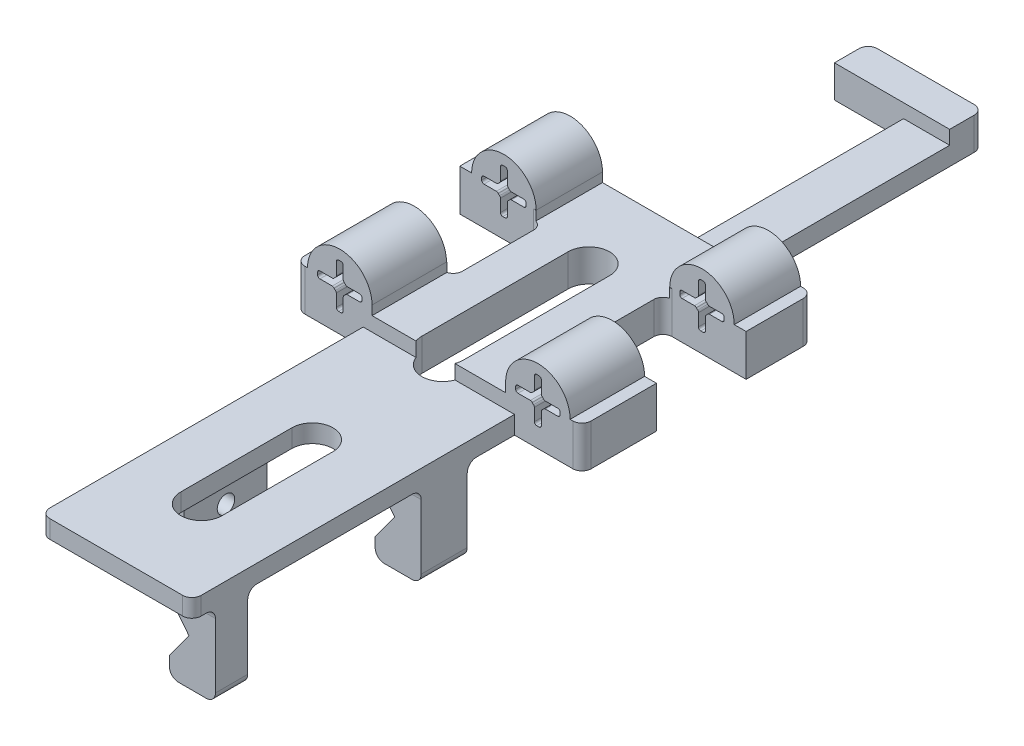
SolidWorks part; units mm, degrees
ref_plane "Спереди" through (0, 0, 0) normal (0, 0, 1) x (1, 0, 0)
ref_plane "Сверху" through (0, 0, 0) normal (0, 1, 0) x (1, 0, 0)
ref_plane "Справа" through (0, 0, 0) normal (1, 0, 0) x (0, 0, -1)
sketch "Эскиз1" plane through (0, 0, 0) normal (0, 0, 1) x (1, 0, 0)
  line L1 (23.3172, -4.25) -> (20.6248, -4.25)
  line L2 (23.8172, -5) -> (23.8172, -4.75)
  line L3 (23.8172, -4.75) -> (23.8172, -5.25)
  line L5 (20.6248, -5.75) -> (23.3172, -5.75)
  line L7 (18.75, -0.1828) -> (19.25, -0.1828)
  line L8 (9.4232, -10) -> (9.4232, -5)
  line L9 (71.5571, -10) -> (71.5571, -5)
  line L10 (12, -5) -> (9.4232, -5)
  line L11 (9.4232, -5) -> (9.4232, -14)
  line L12 (9.4232, -14) -> (71.5571, -14)
  line L13 (71.5571, -14) -> (71.5571, -5)
  line L14 (71.5571, -5) -> (68.9803, -5)
  line L15 (26, -5) -> (54.9803, -5)
  line L16 (19.75, -9.3172) -> (19.75, -6.6248)
  line L18 (19, -9.8172) -> (19.25, -9.8172)
  line L19 (19, -0.1828) -> (18.75, -0.1828)
  line L20 (18.25, -0.6828) -> (18.25, -3.3752)
  line L21 (19.25, -9.8172) -> (18.75, -9.8172)
  line L22 (19.75, -3.3752) -> (19.75, -0.6828)
  line L25 (18.25, -6.6248) -> (18.25, -9.3172)
  line L26 (14.6828, -5.75) -> (17.3752, -5.75)
  line L27 (14.1828, -5) -> (14.1828, -5.25)
  line L28 (14.1828, -5.25) -> (14.1828, -4.75)
  line L30 (17.3752, -4.25) -> (14.6828, -4.25)
  line L31 (63.6051, -4.25) -> (66.2975, -4.25)
  line L33 (66.7975, -5.25) -> (66.7975, -4.75)
  line L34 (66.7975, -5) -> (66.7975, -5.25)
  line L35 (66.2975, -5.75) -> (63.6051, -5.75)
  line L36 (62.7303, -6.6248) -> (62.7303, -9.3172)
  line L39 (61.2303, -3.3752) -> (61.2303, -0.6828)
  line L40 (61.7303, -9.8172) -> (62.2303, -9.8172)
  line L41 (62.7303, -0.6828) -> (62.7303, -3.3752)
  line L42 (61.9803, -0.1828) -> (62.2303, -0.1828)
  line L43 (61.9803, -9.8172) -> (61.7303, -9.8172)
  line L45 (61.2303, -9.3172) -> (61.2303, -6.6248)
  line L46 (62.2803, -0.1828) -> (61.7303, -0.1828)
  line L47 (60.3555, -5.75) -> (57.6631, -5.75)
  line L49 (57.1631, -4.75) -> (57.1631, -5.25)
  line L50 (57.1631, -5) -> (57.1631, -4.75)
  line L51 (57.6631, -4.25) -> (60.3555, -4.25)
  arc A0 (17.7715, -4.0549) -> (18.0549, -3.7715) centre (19, -5) cw
  arc A1 (26, -5) -> (12, -5) centre (19, -5) ccw
  arc A2 (14.1828, -4.75) -> (14.6828, -4.25) centre (14.6828, -4.75) cw
  arc A3 (19.9451, -3.7715) -> (20.2285, -4.0549) centre (19, -5) cw
  arc A4 (20.2285, -5.9451) -> (19.9451, -6.2285) centre (19, -5) cw
  arc A5 (18.0549, -6.2285) -> (17.7715, -5.9451) centre (19, -5) cw
  arc A6 (17.3752, -5.75) -> (17.7715, -5.9451) centre (17.3752, -6.25) cw
  arc A7 (18.25, -6.6248) -> (18.0549, -6.2285) centre (17.75, -6.6248) ccw
  arc A8 (19.75, -6.6248) -> (19.9451, -6.2285) centre (20.25, -6.6248) cw
  arc A9 (20.6248, -5.75) -> (20.2285, -5.9451) centre (20.6248, -6.25) ccw
  arc A10 (20.6248, -4.25) -> (20.2285, -4.0549) centre (20.6248, -3.75) cw
  arc A11 (19.9451, -3.7715) -> (19.75, -3.3752) centre (20.25, -3.3752) cw
  arc A12 (18.25, -3.3752) -> (18.0549, -3.7715) centre (17.75, -3.3752) cw
  arc A13 (17.3752, -4.25) -> (17.7715, -4.0549) centre (17.3752, -3.75) ccw
  arc A14 (63.6051, -4.25) -> (63.2088, -4.0549) centre (63.6051, -3.75) cw
  arc A15 (62.7303, -3.3752) -> (62.9254, -3.7715) centre (63.2303, -3.3752) ccw
  arc A16 (61.0352, -3.7715) -> (61.2303, -3.3752) centre (60.7303, -3.3752) ccw
  arc A17 (60.3555, -4.25) -> (60.7518, -4.0549) centre (60.3555, -3.75) ccw
  arc A18 (60.3555, -5.75) -> (60.7518, -5.9451) centre (60.3555, -6.25) cw
  arc A19 (61.2303, -6.6248) -> (61.0352, -6.2285) centre (60.7303, -6.6248) ccw
  arc A20 (62.7303, -6.6248) -> (62.9254, -6.2285) centre (63.2303, -6.6248) cw
  arc A21 (63.6051, -5.75) -> (63.2088, -5.9451) centre (63.6051, -6.25) ccw
  arc A22 (62.9254, -6.2285) -> (63.2088, -5.9451) centre (61.9803, -5) ccw
  arc A23 (60.7518, -5.9451) -> (61.0352, -6.2285) centre (61.9803, -5) ccw
  arc A24 (61.0352, -3.7715) -> (60.7518, -4.0549) centre (61.9803, -5) ccw
  arc A25 (63.2088, -4.0549) -> (62.9254, -3.7715) centre (61.9803, -5) ccw
  arc A26 (54.9803, -5) -> (68.9803, -5) centre (61.9803, -5) cw
  arc A27 (14.1828, -5.25) -> (14.6828, -5.75) centre (14.6828, -5.25) ccw
  arc A28 (18.75, -9.8172) -> (18.25, -9.3172) centre (18.75, -9.3172) cw
  arc A29 (19.25, -9.8172) -> (19.75, -9.3172) centre (19.25, -9.3172) ccw
  arc A30 (23.8172, -5.25) -> (23.3172, -5.75) centre (23.3172, -5.25) cw
  arc A31 (23.8172, -4.75) -> (23.3172, -4.25) centre (23.3172, -4.75) ccw
  arc A32 (18.75, -0.1828) -> (18.25, -0.6828) centre (18.75, -0.6828) ccw
  arc A33 (19.25, -0.1828) -> (19.75, -0.6828) centre (19.25, -0.6828) cw
  arc A34 (61.7303, -9.8172) -> (61.2303, -9.3172) centre (61.7303, -9.3172) cw
  arc A35 (62.2303, -9.8172) -> (62.7303, -9.3172) centre (62.2303, -9.3172) ccw
  arc A36 (66.7975, -5.25) -> (66.2975, -5.75) centre (66.2975, -5.25) cw
  arc A37 (57.1631, -5.25) -> (57.6631, -5.75) centre (57.6631, -5.25) ccw
  arc A38 (57.1631, -4.75) -> (57.6631, -4.25) centre (57.6631, -4.75) cw
  arc A39 (61.7303, -0.1828) -> (61.2303, -0.6828) centre (61.7303, -0.6828) ccw
  arc A40 (62.2303, -0.1828) -> (62.7303, -0.6828) centre (62.2303, -0.6828) cw
  arc A41 (66.7975, -4.75) -> (66.2975, -4.25) centre (66.2975, -4.75) ccw
  point P49 (19, -5)
  point P59 (19.75, -3.6435)
  point P109 (61.2303, -3.6435)
  dimension "D1" = 4
  dimension "D2" = 0.5
  dimension "D3" = 0.5
extrude "Бобышка-Вытянуть1" add sketch "Эскиз1" along normal blind 50
ref_plane "Плоскость1" through (0, 5, 0) normal (0, 1, 0) x (1, 0, 0)
sketch "Эскиз3" plane through (0, 5, 0) normal (0, 1, 0) x (1, 0, 0)
  line L1 (7.4576, -14.3929) -> (74.5504, -14.3929)
  line L2 (7.4576, -14.3929) -> (7.4576, -33.8454)
  line L3 (7.4576, -33.8454) -> (74.5504, -33.8454)
  line L4 (74.5504, -14.3929) -> (74.5504, -33.8454)
extrude "Вырез-Вытянуть1" cut sketch "Эскиз3" against normal blind 10
fillet "Скругление1" radius 2 4 edges at (9.4232, -9.5, 0) (71.5571, -9.5, 0) (71.5571, -9.5, 50) (9.4232, -9.5, 50)
ref_plane "Плоскость2" through (0, 5, 0) normal (0, 1, 0) x (1, 0, 0)
sketch "Эскиз4" plane through (0, 5, 0) normal (0, 1, 0) x (1, 0, 0)
  line L0 (12, -14.3929) -> (25.4537, -14.3929)
  line L1 (12, -33.8454) -> (25.4537, -33.8454)
  line L2 (27.4537, -31.8454) -> (27.4537, -16.3929)
  line L3 (12, -14.3929) -> (9.4232, -14.3929)
  line L4 (9.4232, -48) -> (9.4232, -2) construction
  line L5 (9.4232, -14.3929) -> (9.4232, -33.8454)
  line L6 (9.4232, -33.8454) -> (12, -33.8454)
  line L7 (40.4901, -1000) -> (40.4901, 49000) construction
  line L8 (26, 0) -> (54.9803, 0) construction
  line L9 (71.5571, -33.8454) -> (68.9803, -33.8454)
  line L10 (68.9803, -33.8454) -> (55.5266, -33.8454)
  line L11 (53.5266, -31.8454) -> (53.5266, -16.3929)
  line L12 (68.9803, -14.3929) -> (55.5266, -14.3929)
  line L13 (68.9803, -14.3929) -> (71.5571, -14.3929)
  line L14 (71.5571, -14.3929) -> (71.5571, -33.8454)
  arc A0 (53.5266, -31.8454) -> (55.5266, -33.8454) centre (55.5266, -31.8454) ccw
  arc A1 (53.5266, -16.3929) -> (55.5266, -14.3929) centre (55.5266, -16.3929) cw
  arc A2 (25.4537, -33.8454) -> (27.4537, -31.8454) centre (25.4537, -31.8454) ccw
  arc A3 (27.4537, -16.3929) -> (25.4537, -14.3929) centre (25.4537, -16.3929) ccw
  point P15 (40.4901, 0)
  point P23 (53.5266, -33.8454)
  point P26 (53.5266, -14.3929)
  point P29 (27.4537, -33.8454)
  point P32 (27.4537, -14.3929)
  dimension "D1" = 2
extrude "Вырез-Вытянуть2" cut sketch "Эскиз4" against normal blind 30
sketch "Эскиз5" plane through (0, 0, 50) normal (0, 0, 1) x (1, 0, 0)
  line L0 (24.0789, -14) -> (24.0789, -10.1)
  line L1 (11.4232, -14) -> (69.5571, -14) construction
  line L2 (24.0789, -10.1) -> (56.9191, -10.1)
  line L3 (56.9191, -10.1) -> (56.9191, -14)
  line L4 (56.9191, -14) -> (24.0789, -14)
extrude "Бобышка-Вытянуть2" add sketch "Эскиз5" along normal blind 70
sketch "Эскиз7" plane through (0, 5, 0) normal (0, 1, 0) x (1, 0, 0)
  line L0 (56.9191, -50) -> (24.0789, -50) construction
  line L1 (26, 0) -> (54.9803, 0)
  line L2 (26, 0) -> (26, -50)
  line L3 (26, -50) -> (54.9803, -50)
  line L4 (54.9803, 0) -> (54.9803, -50)
  line L5 (26, -50) -> (54.9803, -50) construction
extrude "Вырез-Вытянуть3" cut sketch "Эскиз7" against normal blind 12
ref_plane "Плоскость4" through (0, -24, 0) normal (0, -1, 0) x (-1, 0, 0)
sketch "Эскиз9" plane through (0, -24, 0) normal (0, -1, 0) x (-1, 0, 0)
  line L0 (-24.0789, -114.8996) -> (-24.0789, -69.8111)
  line L1 (-24.0789, -120) -> (-24.0789, -50) construction
  line L2 (-24.0789, -69.8111) -> (-56.9191, -69.8111)
  line L3 (-56.9191, -120) -> (-56.9191, -50) construction
  line L4 (-56.9191, -69.8111) -> (-56.9191, -114.8996)
  line L5 (-56.9191, -114.8996) -> (-24.0789, -114.8996)
ref_plane "Плоскость5" through (0, -14, 0) normal (0, -1, 0) x (-1, 0, 0)
sketch "Эскиз10" plane through (0, -14, 0) normal (0, -1, 0) x (-1, 0, 0)
  line L0 (-30.2022, -94.9727) -> (-30.2022, -76.9727)
  line L1 (-30.2022, -76.9727) -> (-24.0789, -76.9727)
  line L2 (-24.0789, -120) -> (-24.0789, -50) construction
  line L3 (-24.0789, -76.9727) -> (-24.0789, -94.9727)
  line L4 (-24.0789, -94.9727) -> (-30.2022, -94.9727)
extrude "Бобышка-Вытянуть4" add sketch "Эскиз10" along normal blind 18
fillet "Скругление6" radius 3 3 edges at (27.1405, -14, 94.9727) (27.1405, -14, 76.9727) (30.2022, -14, 85.9727)
sketch "Эскиз15" plane through (0, 0, 0) normal (0, 0, -1) x (-1, 0, 0)
  line L0 (-61.3072, -14) -> (-41.1958, -14)
  line L1 (-34.1736, -14) -> (34.1736, -14) construction
  line L2 (-53.6559, -10) -> (-43.6559, -10)
  line L3 (-43.6559, -10) -> (-43.6559, -14)
  line L4 (-43.6559, -14) -> (-53.6559, -14)
  line L5 (-34.1958, -14) -> (-49.6559, -14)
  line L8 (-33.1958, -14) -> (-49.6559, -14)
  line L9 (-49.6559, -10) -> (-53.6559, -10)
  line L10 (-53.6559, -10) -> (-53.6559, -14)
  line L11 (-53.6559, -14) -> (-49.6559, -14)
extrude "Бобышка-Вытянуть7" add sketch "Эскиз15" along normal blind 55 contours L2 L10 L0 L4 L3
sketch "Эскиз17" plane through (0, -14, 0) normal (0, -1, 0) x (1, 0, 0)
  line L0 (53.6559, -55) -> (28.6559, -55)
  line L1 (28.6559, -55) -> (28.6559, -47.6728)
  line L2 (28.6559, -47.6728) -> (53.6559, -47.6728)
  line L3 (53.6559, -55) -> (53.6559, 0) construction
  line L4 (53.6559, -47.6728) -> (53.6559, -55)
extrude "Бобышка-Вытянуть8" add sketch "Эскиз17" against normal blind 7 contours L2 L4 L0 L1
sketch "Эскиз18" plane through (0, -14, 0) normal (0, -1, 0) x (-1, 0, 0)
  line L0 (-56.9191, -114.8996) -> (-46.9191, -114.8996)
  line L1 (-56.9191, -114.8996) -> (-24.0789, -114.8996) construction
  line L2 (-46.9191, -114.8996) -> (-46.9191, -107.8996)
  line L3 (-46.9191, -107.8996) -> (-56.9191, -107.8996)
  line L4 (-56.9191, -69.8111) -> (-56.9191, -114.8996) construction
  line L5 (-56.9191, -107.8996) -> (-56.9191, -114.8996)
  line L6 (-46.9191, -70.2474) -> (-56.9191, -70.2474)
  line L7 (-56.9191, -70.2474) -> (-56.9191, -60.2632)
  line L8 (-56.9191, -120) -> (-56.9191, -50) construction
  line L9 (-56.9191, -60.2632) -> (-46.9191, -60.2632)
  line L10 (-46.9191, -60.2632) -> (-46.9191, -70.2474)
extrude "Бобышка-Вытянуть9" add sketch "Эскиз18" along normal blind 18
sketch "Эскиз19" plane through (0, 0, 114.8996) normal (0, 0, 1) x (1, 0, 0)
  line L0 (46.9191, -14) -> (46.9191, -16.7884)
  line L1 (46.9191, -32) -> (46.9191, -14) construction
  line L2 (46.9191, -16.7884) -> (51.1663, -22.097)
  line L3 (51.1663, -22.097) -> (46.9191, -27.9436)
  line L4 (46.9191, -27.9436) -> (46.9191, -36)
  line L5 (46.9191, -36) -> (46.9191, -16.7884)
  line M2 (46.9191, -14) -> (46.9191, -32)
extrude "Вырез-Вытянуть4" cut sketch "Эскиз19" against normal blind 60 contours L3 L2 M2
fillet "Скругление7" radius 2 6 edges at (51.9191, -14, 60.2632) (46.9191, -14, 65.2553) (51.9191, -14, 70.2474) (51.9191, -14, 107.8996) (46.9191, -14, 111.3996) (51.9191, -14, 114.8996)
sketch "Эскиз20" plane through (24.0789, 0, 0) normal (-1, 0, 0) x (0, 0, 1)
  circle A0 centre (85.8943, -22.3625) radius 1.9
  point P2 (0, 0)
  point P3 (86.0272, -21.8105)
  point P4 (85.9996, -20.9605)
  point P5 (0, 0)
  point P6 (85.919, -21.8437)
  point P7 (0, 0)
  point P8 (85.8943, -22.3625)
extrude "Вырез-Вытянуть5" cut sketch "Эскиз20" against normal blind 13
fillet "Скругление8" radius 2 6 edges at (46.9191, -32, 111.3996) (56.9191, -32, 111.3996) (56.9191, -32, 65.2553) (46.9191, -32, 65.2553) (27.1405, -32, 76.9727) (27.1405, -32, 94.9727)
sketch "Эскиз21" plane through (0, -14, 0) normal (0, -1, 0) x (1, 0, 0)
  line L0 (35.2736, 100.7651) -> (35.2736, 76.6845)
  line L2 (44.2173, 76.6845) -> (44.2173, 100.7651)
  arc A0 (44.2173, 100.7651) -> (35.2736, 100.7651) centre (39.7454, 100.7651) ccw
  arc A1 (35.2736, 76.6845) -> (44.2173, 76.6845) centre (39.7454, 76.6845) ccw
extrude "Вырез-Вытянуть6" cut sketch "Эскиз21" against normal blind 13
fillet "Скругление9" radius 2 2 edges at (24.0789, -12.05, 120) (56.9191, -12.05, 120)
sketch "Эскиз22" plane through (0, -14, 0) normal (0, -1, 0) x (1, 0, 0)
  line L0 (35.2651, 48.445) -> (35.2651, 16.7368)
  line L2 (44.2651, 16.7368) -> (44.2651, 48.445)
  arc A0 (44.2651, 48.445) -> (35.2651, 48.445) centre (39.7651, 48.445) ccw
  arc A1 (35.2651, 16.7368) -> (44.2651, 16.7368) centre (39.7651, 16.7368) ccw
  point P1 (39.7651, 16.7368)
extrude "Вырез-Вытянуть7" cut sketch "Эскиз22" against normal blind 13
fillet "Скругление10" radius 2 2 edges at (28.6559, -10.5, -55) (53.6559, -10.5, -55)
